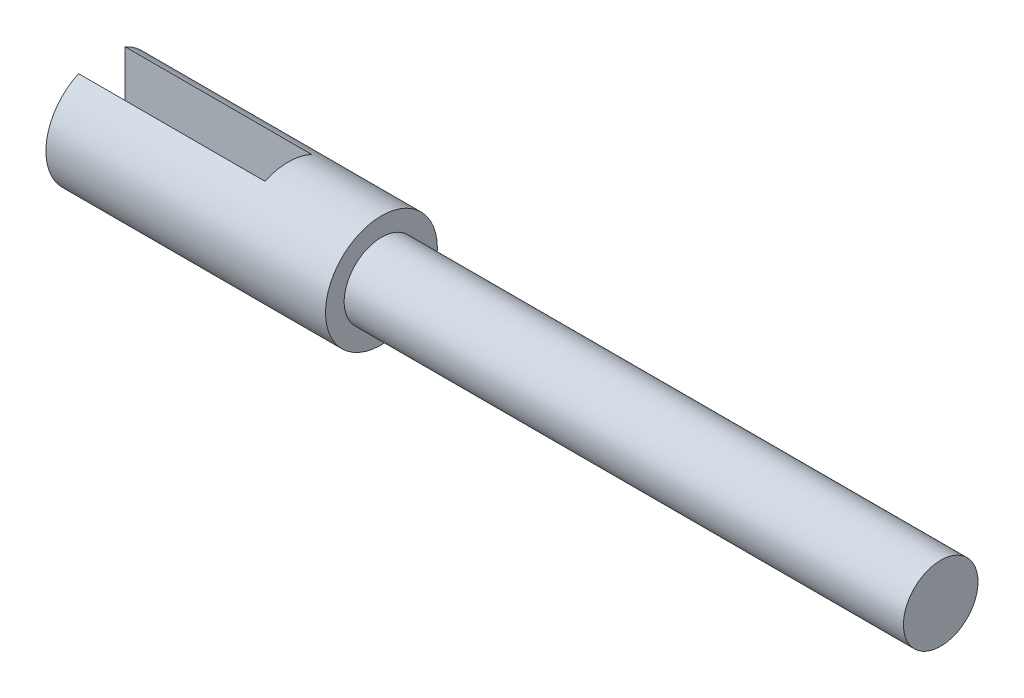
SolidWorks part; units mm, degrees
ref_plane "Front Plane" through (0, 0, 0) normal (0, 0, 1) x (1, 0, 0)
ref_plane "Top Plane" through (0, 0, 0) normal (0, 1, 0) x (1, 0, 0)
ref_plane "Right Plane" through (0, 0, 0) normal (1, 0, 0) x (0, 0, -1)
sketch "Sketch1" plane through (0, 0, 0) normal (1, 0, 0) x (0, 0, -1)
  circle A0 centre (0, 0) radius 2.54
  dimension "D1" = 5.08
extrude "Boss-Extrude1" add sketch "Sketch1" along normal blind 38.1
sketch "Sketch2" plane through (0, 0, 0) normal (1, 0, 0) x (0, 0, -1)
  circle A0 centre (0, 0) radius 3.81
  dimension "D1" = 7.62
extrude "Boss-Extrude2" add sketch "Sketch2" against normal blind 19.05 contours A0
sketch "Sketch3" plane through (0, 0, 0) normal (0, 1, 0) x (1, 0, 0)
  line L0 (-19.05, 3.81) -> (-19.05, -3.81) construction
  line L1 (-19.05, 1.5875) -> (-6.35, 1.5875)
  line L2 (-19.05, 1.5875) -> (-19.05, -1.5875)
  line L3 (-19.05, -1.5875) -> (-6.35, -1.5875)
  line L4 (-6.35, 1.5875) -> (-6.35, -1.5875)
  line L5 (-19.05, 0) -> (-6.35, 0) construction
  dimension "D1" = 12.7
  dimension "D2" = 3.175
extrude "Cut-Extrude1" cut sketch "Sketch3" against normal through all both and the other way through all
